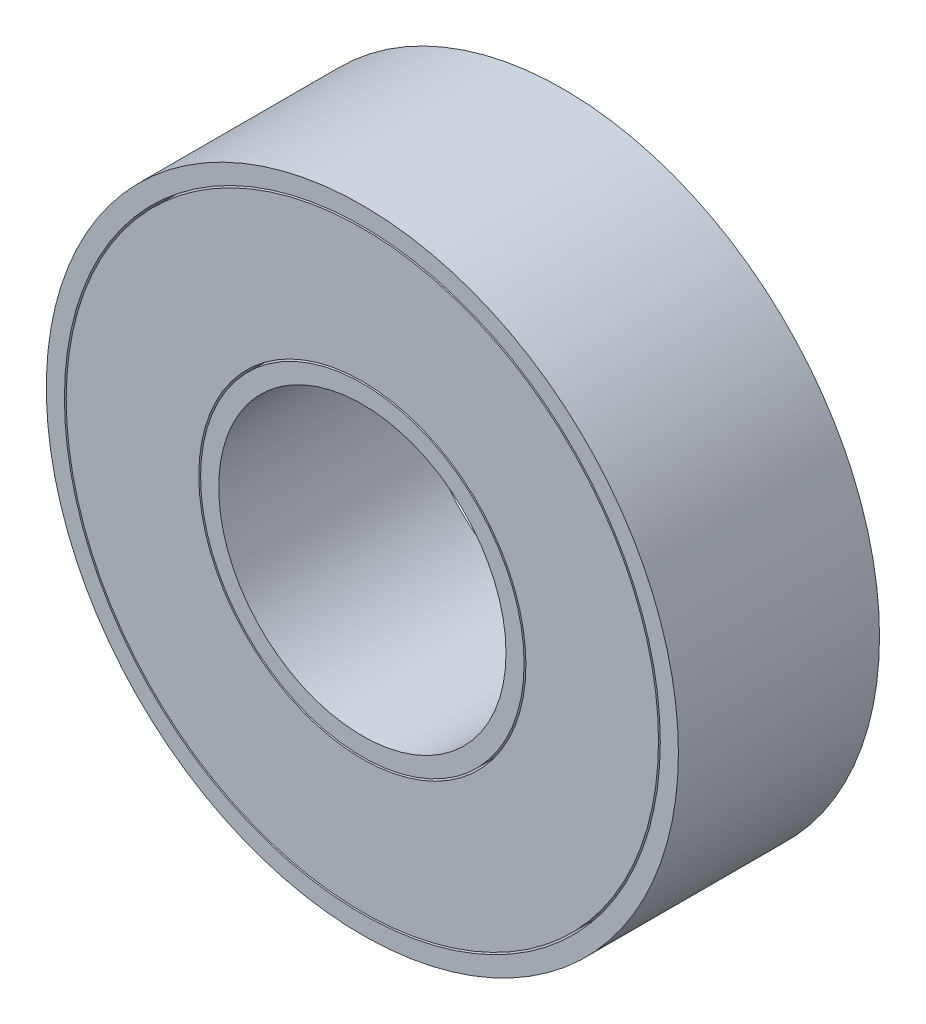
SolidWorks part; units mm, degrees
material "Acero aleado fundido"
ref_plane "Alzado" through (0, 0, 0) normal (0, 0, 1) x (1, 0, 0)
ref_plane "Planta" through (0, 0, 0) normal (0, 1, 0) x (1, 0, 0)
ref_plane "Vista lateral" through (0, 0, 0) normal (1, 0, 0) x (0, 0, -1)
sketch "Croquis1" plane through (0, 0, 0) normal (0, 0, 1) x (1, 0, 0)
  circle A0 centre (0, 0) radius 7.9375
  circle A1 centre (0, 0) radius 17.4625
  dimension "D1" = 34.925
  dimension "D2" = 15.875
extrude "Saliente-Extruir1" add sketch "Croquis1" along normal blind 11.112
sketch "Croquis5" plane through (0, 0, 0) normal (0, 0, -1) x (-1, 0, 0)
  circle A0 centre (0, 0) radius 9.0375
  circle A1 centre (0, 0) radius 8.9375
  circle A2 centre (0, 0) radius 16.3625
  circle A3 centre (0, 0) radius 16.4625
  circle A4 centre (0, 0) radius 17.4625 construction
  circle A5 centre (0, 0) radius 7.9375 construction
  dimension "D1" = 1.1
  dimension "D2" = 1
  dimension "D3" = 0.1
  dimension "D4" = 1
extrude "Cortar-Extruir4" cut sketch "Croquis5" against normal blind 20.5 contours A0 A1 | A3 A2
